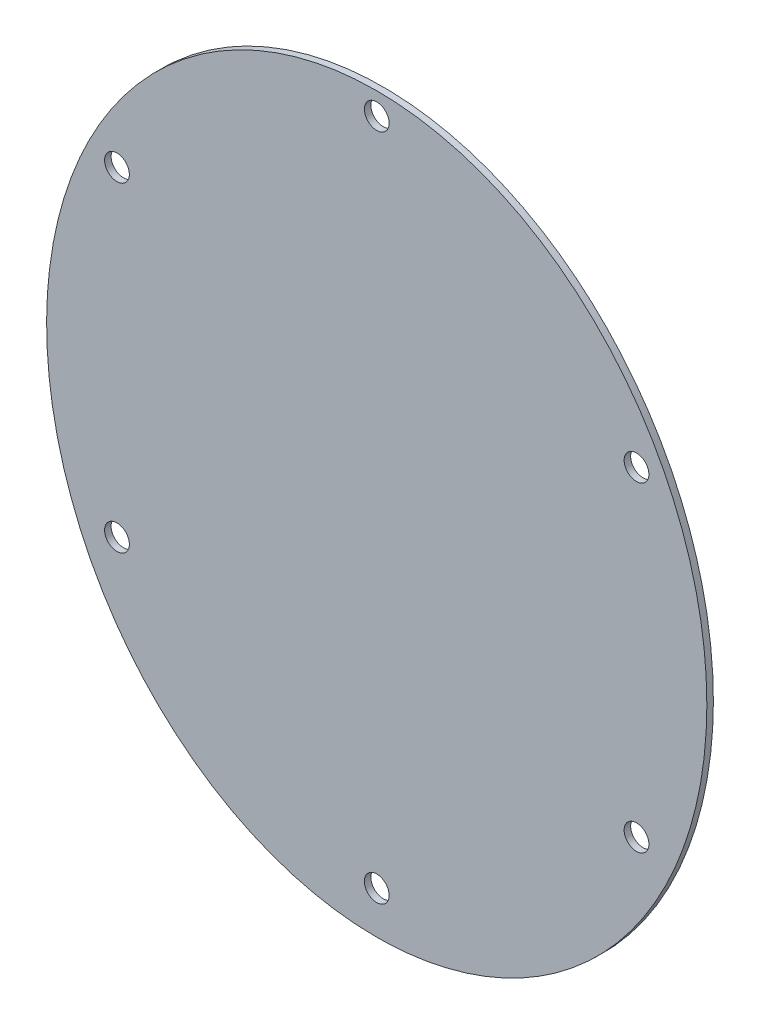
SolidWorks part; units mm, degrees
material "FR-4 / G-10"
ref_plane "Front Plane" through (0, 0, 0) normal (0, 0, 1) x (1, 0, 0)
ref_plane "Top Plane" through (0, 0, 0) normal (0, 1, 0) x (1, 0, 0)
ref_plane "Right Plane" through (0, 0, 0) normal (1, 0, 0) x (0, 0, -1)
sketch "Sketch2" plane through (0, 0, 0) normal (0, 0, 1) x (1, 0, 0)
  spline S2 degree 3 poles (-0.982, -59.5031) (3.4369, -59.5126) (6.9024, -59.1135) (12.0016, -57.9369) (13.6848, -57.4476) (17.017, -56.2704) (18.6346, -55.5938) (23.3506, -53.3146) (26.3141, -51.4645) (31.883, -47.1216) (34.3993, -44.6988) (37.8082, -40.7216) (38.883, -39.3383) (40.4034, -37.1771) (40.8939, -36.4435) (41.8355, -34.9617) (42.2877, -34.2119) (44.4588, -30.4199) (45.9095, -27.2493) (47.6718, -22.2954) (48.1916, -20.6043) (49.0752, -17.2108) (49.4413, -15.5038) (50.3226, -10.3533) (50.6207, -6.8803) (50.626, -2.4893) (50.6086, -1.6067) (50.5366, 0.1496) (50.3733, 2.7733) (50.0458, 5.365) (49.1766, 10.5069) (48.312, 13.8793) (46.8525, 18.0213) (46.5408, 18.8479) (45.8844, 20.4781) (45.5393, 21.2831) (44.4535, 23.6674) (43.6622, 25.2164) (41.088, 29.7424) (39.1053, 32.5991) (36.26, 35.9487) (35.6711, 36.609) (34.469, 37.8915) (33.8546, 38.5153) (31.9711, 40.3346) (30.6618, 41.4778) (27.9361, 43.6253) (26.5195, 44.6291) (24.3102, 46.0256) (23.5598, 46.4728) (22.0297, 47.3294) (21.2483, 47.7397) (17.2857, 49.683) (14.0077, 50.8633) (8.929, 52.0729) (7.209, 52.3822) (4.5864, 52.6981) (3.7034, 52.7786) (1.947, 52.8876) (1.0708, 52.9165) (-3.3004, 52.9354) (-6.7662, 52.5525) (-11.0591, 51.5719) (-11.9172, 51.35) (-13.6082, 50.8609) (-14.4437, 50.5933) (-16.9205, 49.7234) (-18.5325, 49.0541) (-21.6804, 47.5417) (-23.2165, 46.6992) (-25.4631, 45.3041) (-26.202, 44.8172) (-27.6444, 43.8111) (-28.3501, 43.2907) (-31.8038, 40.6052) (-34.3281, 38.19) (-37.1976, 34.8514) (-37.7577, 34.1667) (-38.8385, 32.7784) (-39.3606, 32.0735) (-40.8736, 29.9272) (-41.8113, 28.4544) (-43.5498, 25.4281) (-44.3511, 23.8749) (-45.4508, 21.4845) (-45.8002, 20.6777) (-46.4649, 19.0437) (-46.7786, 18.2204) (-48.2517, 14.0868) (-49.1306, 10.7115) (-50.0197, 5.5507) (-50.2444, 3.8141) (-50.471, 1.1839) (-50.528, 0.3022) (-50.6043, -1.4537) (-50.6237, -2.3299) (-50.6298, -6.7017) (-50.3434, -10.1708) (-49.4755, -15.3319) (-49.1133, -17.0451) (-48.4543, -19.6038) (-48.2155, -20.4539) (-47.704, -22.1336) (-47.4308, -22.9652) (-45.9788, -27.0827) (-44.543, -30.2475) (-41.9616, -34.7931) (-41.03, -36.2748) (-39.5173, -38.443) (-38.9943, -39.1558) (-37.9217, -40.5465) (-37.3706, -41.2265) (-34.543, -44.5507) (-32.0492, -46.9678) (-28.6243, -49.6677) (-27.9239, -50.1916) (-26.4908, -51.2055) (-25.7564, -51.6968) (-23.5153, -53.1105) (-21.9852, -53.9643) (-17.2881, -56.263) (-14.0155, -57.4482) (-9.7356, -58.4646) (-8.8676, -58.6449) (-7.1275, -58.9539) (-6.2548, -59.083) (-4.5045, -59.2907) (-3.6268, -59.3692) (-1.8663, -59.4754) (-0.982, -59.5031) (3.4369, -59.5126) (6.9024, -59.1135) knots -0.007813 -0.007813 0 0 0.03125 0.03125 0.046875 0.046875 0.0625 0.0625 0.09375 0.09375 0.125 0.125 0.140625 0.140625 0.148437 0.148437 0.15625 0.15625 0.1875 0.1875 0.203125 0.203125 0.21875 0.21875 0.25 0.25 0.257812 0.257812 0.265625 0.28125 0.28125 0.3125 0.3125 0.320312 0.320312 0.328125 0.328125 0.34375 0.34375 0.375 0.375 0.382812 0.382812 0.390625 0.390625 0.40625 0.40625 0.421875 0.421875 0.429687 0.429687 0.4375 0.4375 0.46875 0.46875 0.484375 0.484375 0.492187 0.492187 0.5 0.5 0.53125 0.53125 0.539062 0.539062 0.546875 0.546875 0.5625 0.5625 0.578125 0.578125 0.585937 0.585937 0.59375 0.59375 0.625 0.625 0.632812 0.632812 0.640625 0.640625 0.65625 0.65625 0.671875 0.671875 0.679687 0.679687 0.6875 0.6875 0.71875 0.71875 0.734375 0.734375 0.742187 0.742187 0.75 0.75 0.78125 0.78125 0.796875 0.796875 0.804687 0.804687 0.8125 0.8125 0.84375 0.84375 0.859375 0.859375 0.867187 0.867187 0.875 0.875 0.90625 0.90625 0.914062 0.914062 0.921875 0.921875 0.9375 0.9375 0.96875 0.96875 0.976562 0.976562 0.984375 0.984375 0.992187 0.992187 1 1 1.03125 1.03125 1.046875 only from (-0.0982, -59.505) to (-0.0982, -59.505)
  spline S3 degree 3 poles (-0.982, -59.5031) (3.4369, -59.5126) (6.9024, -59.1135) (12.0016, -57.9369) (13.6848, -57.4476) (17.017, -56.2704) (18.6346, -55.5938) (23.3506, -53.3146) (26.3141, -51.4645) (31.883, -47.1216) (34.3993, -44.6988) (37.8082, -40.7216) (38.883, -39.3383) (40.4034, -37.1771) (40.8939, -36.4435) (41.8355, -34.9617) (42.2877, -34.2119) (44.4588, -30.4199) (45.9095, -27.2493) (47.6718, -22.2954) (48.1916, -20.6043) (49.0752, -17.2108) (49.4413, -15.5038) (50.3226, -10.3533) (50.6207, -6.8803) (50.626, -2.4893) (50.6086, -1.6067) (50.5366, 0.1496) (50.3733, 2.7733) (50.0458, 5.365) (49.1766, 10.5069) (48.312, 13.8793) (46.8525, 18.0213) (46.5408, 18.8479) (45.8844, 20.4781) (45.5393, 21.2831) (44.4535, 23.6674) (43.6622, 25.2164) (41.088, 29.7424) (39.1053, 32.5991) (36.26, 35.9487) (35.6711, 36.609) (34.469, 37.8915) (33.8546, 38.5153) (31.9711, 40.3346) (30.6618, 41.4778) (27.9361, 43.6253) (26.5195, 44.6291) (24.3102, 46.0256) (23.5598, 46.4728) (22.0297, 47.3294) (21.2483, 47.7397) (17.2857, 49.683) (14.0077, 50.8633) (8.929, 52.0729) (7.209, 52.3822) (4.5864, 52.6981) (3.7034, 52.7786) (1.947, 52.8876) (1.0708, 52.9165) (-3.3004, 52.9354) (-6.7662, 52.5525) (-11.0591, 51.5719) (-11.9172, 51.35) (-13.6082, 50.8609) (-14.4437, 50.5933) (-16.9205, 49.7234) (-18.5325, 49.0541) (-21.6804, 47.5417) (-23.2165, 46.6992) (-25.4631, 45.3041) (-26.202, 44.8172) (-27.6444, 43.8111) (-28.3501, 43.2907) (-31.8038, 40.6052) (-34.3281, 38.19) (-37.1976, 34.8514) (-37.7577, 34.1667) (-38.8385, 32.7784) (-39.3606, 32.0735) (-40.8736, 29.9272) (-41.8113, 28.4544) (-43.5498, 25.4281) (-44.3511, 23.8749) (-45.4508, 21.4845) (-45.8002, 20.6777) (-46.4649, 19.0437) (-46.7786, 18.2204) (-48.2517, 14.0868) (-49.1306, 10.7115) (-50.0197, 5.5507) (-50.2444, 3.8141) (-50.471, 1.1839) (-50.528, 0.3022) (-50.6043, -1.4537) (-50.6237, -2.3299) (-50.6298, -6.7017) (-50.3434, -10.1708) (-49.4755, -15.3319) (-49.1133, -17.0451) (-48.4543, -19.6038) (-48.2155, -20.4539) (-47.704, -22.1336) (-47.4308, -22.9652) (-45.9788, -27.0827) (-44.543, -30.2475) (-41.9616, -34.7931) (-41.03, -36.2748) (-39.5173, -38.443) (-38.9943, -39.1558) (-37.9217, -40.5465) (-37.3706, -41.2265) (-34.543, -44.5507) (-32.0492, -46.9678) (-28.6243, -49.6677) (-27.9239, -50.1916) (-26.4908, -51.2055) (-25.7564, -51.6968) (-23.5153, -53.1105) (-21.9852, -53.9643) (-17.2881, -56.263) (-14.0155, -57.4482) (-9.7356, -58.4646) (-8.8676, -58.6449) (-7.1275, -58.9539) (-6.2548, -59.083) (-4.5045, -59.2907) (-3.6268, -59.3692) (-1.8663, -59.4754) (-0.982, -59.5031) (3.4369, -59.5126) (6.9024, -59.1135) knots -0.007813 -0.007813 0 0 0.03125 0.03125 0.046875 0.046875 0.0625 0.0625 0.09375 0.09375 0.125 0.125 0.140625 0.140625 0.148437 0.148437 0.15625 0.15625 0.1875 0.1875 0.203125 0.203125 0.21875 0.21875 0.25 0.25 0.257812 0.257812 0.265625 0.28125 0.28125 0.3125 0.3125 0.320312 0.320312 0.328125 0.328125 0.34375 0.34375 0.375 0.375 0.382812 0.382812 0.390625 0.390625 0.40625 0.40625 0.421875 0.421875 0.429687 0.429687 0.4375 0.4375 0.46875 0.46875 0.484375 0.484375 0.492187 0.492187 0.5 0.5 0.53125 0.53125 0.539062 0.539062 0.546875 0.546875 0.5625 0.5625 0.578125 0.578125 0.585937 0.585937 0.59375 0.59375 0.625 0.625 0.632812 0.632812 0.640625 0.640625 0.65625 0.65625 0.671875 0.671875 0.679687 0.679687 0.6875 0.6875 0.71875 0.71875 0.734375 0.734375 0.742187 0.742187 0.75 0.75 0.78125 0.78125 0.796875 0.796875 0.804687 0.804687 0.8125 0.8125 0.84375 0.84375 0.859375 0.859375 0.867187 0.867187 0.875 0.875 0.90625 0.90625 0.914062 0.914062 0.921875 0.921875 0.9375 0.9375 0.96875 0.96875 0.976562 0.976562 0.984375 0.984375 0.992187 0.992187 1 1 1.03125 1.03125 1.046875 only from (-0.0982, -59.505) to (-0.0982, -59.505)
  dimension "D1" = 1
extrude "Boss-Extrude1" add sketch "Sketch2" along normal blind 1
hole_wizard "#6 Clearance Hole1" positions "Sketch4" profile "Sketch3" hole size "#6" standard "Ansi Inch" end condition through all
sketch "Sketch4" plane through (0, 0, 1) normal (0, 0, 1) x (1, 0, 0)
  point P27 (0, 49.5359)
  point P30 (39.8372, 22.8281)
  point P38 (-39.8372, 22.8281)
  point P41 (-39.8372, -26.2922)
  point P44 (0, -53)
  point P47 (39.8372, -26.2922)
sketch "Sketch3" plane through (0, 49.5359, 1) normal (1, 0, 0) x (0, -1, 0)
  line L0 (0, 0) -> (0, 1.01)
  line L1 (0, 1.01) -> (1.8986, 1.01)
  line L2 (1.8986, 1.01) -> (1.8986, 0)
  line L5 (1.8986, 0) -> (0, 0)
  line L11 (0, -6.35) -> (0, 107.95) construction
  dimension "Thru Hole Dia." = 3.7973
  dimension "Thru Hole Depth" = 1.01
